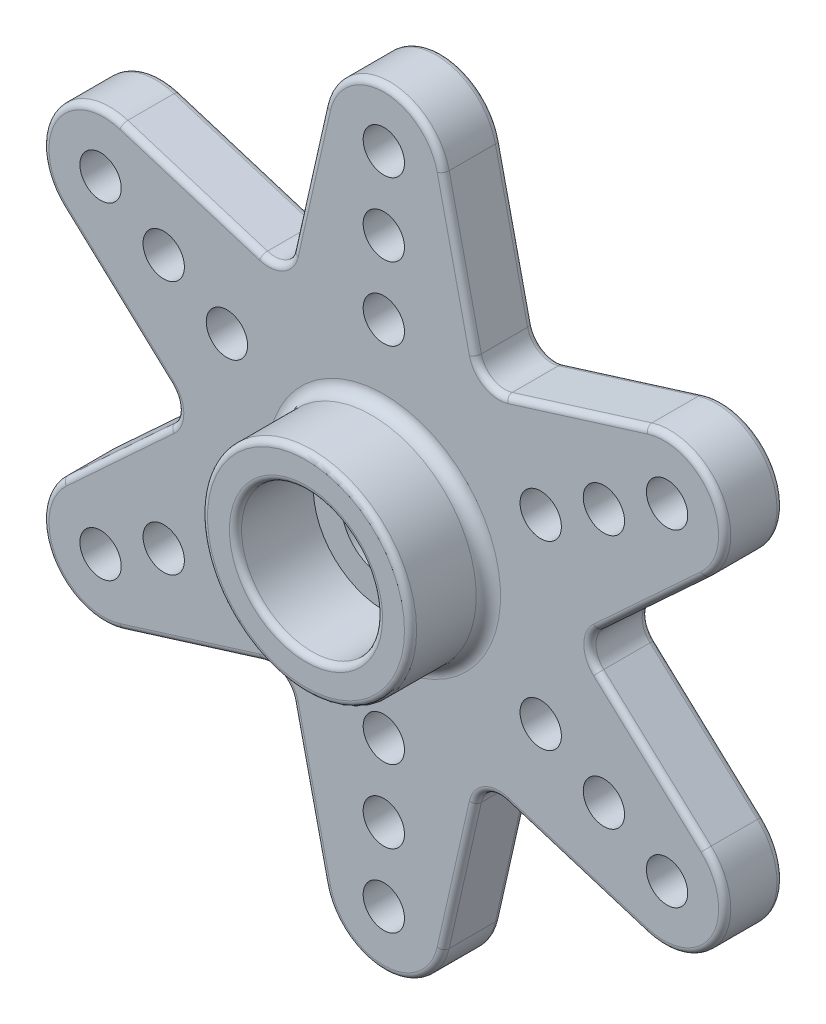
SolidWorks part; units mm, degrees
ref_plane "Front Plane" through (0, 0, 0) normal (0, 0, 1) x (1, 0, 0)
ref_plane "Top Plane" through (0, 0, 0) normal (0, 1, 0) x (1, 0, 0)
ref_plane "Right Plane" through (0, 0, 0) normal (1, 0, 0) x (0, 0, -1)
sketch "Sketch1" plane through (0, 0, 0) normal (0, 0, 1) x (1, 0, 0)
  line L0 (0, 13.3) -> (0, -13.3) construction
  line L1 (-11.5181, 6.65) -> (11.5181, -6.65) construction
  line L2 (11.5181, 6.65) -> (-11.5181, -6.65) construction
  line L3 (-4, -6.9282) -> (-2.4387, -13.8501)
  line L4 (2.4387, 13.8501) -> (4, 6.9282)
  line L5 (4, 6.9282) -> (10.7751, 9.037)
  line L6 (13.2139, 4.813) -> (8, 0)
  line L7 (8, 0) -> (13.2139, -4.813)
  line L8 (10.7751, -9.037) -> (4, -6.9282)
  line L9 (4, -6.9282) -> (2.4387, -13.8501)
  line L10 (-10.7751, -9.037) -> (-4, -6.9282)
  line L11 (-8, 0) -> (-13.2139, -4.813)
  line L12 (-13.2139, 4.813) -> (-8, 0)
  line L13 (-4, 6.9282) -> (-10.7751, 9.037)
  line L14 (-2.4387, 13.8501) -> (-4, 6.9282)
  line L15 (-4, 6.9282) -> (4, 6.9282) construction
  line L16 (-8, 0) -> (-4, 6.9282) construction
  line L17 (-8, 0) -> (-4, -6.9282) construction
  line L18 (-4, -6.9282) -> (4, -6.9282) construction
  arc A0 (-2.4387, 13.8501) -> (2.4387, 13.8501) centre (0, 13.3) cw
  arc A1 (10.7751, 9.037) -> (13.2139, 4.813) centre (11.5181, 6.65) cw
  arc A2 (13.2139, -4.813) -> (10.7751, -9.037) centre (11.5181, -6.65) cw
  arc A3 (2.4387, -13.8501) -> (-2.4387, -13.8501) centre (0, -13.3) cw
  arc A4 (-13.2139, -4.813) -> (-10.7751, -9.037) centre (-11.5181, -6.65) ccw
  arc A5 (-10.7751, 9.037) -> (-13.2139, 4.813) centre (-11.5181, 6.65) ccw
  circle A6 centre (0, 0) radius 1.75
  dimension "D1" = 26.6
  dimension "D2" = 2.5
  dimension "D3" = 8
  dimension "D5" = 3.5
  dimension "D4" = 60
extrude "Boss-Extrude1" add sketch "Sketch1" along normal blind 2.4
sketch "Sketch2" plane through (0, 0, 2.4) normal (0, 0, 1) x (1, 0, 0)
  circle A0 centre (0, 0) radius 4.3
  circle A1 centre (0, 0) radius 2.9
  dimension "D1" = 8.6
  dimension "D2" = 5.8
extrude "Boss-Extrude2" add sketch "Sketch2" along normal blind 3.2
sketch "Sketch4" plane through (0, 0, 0) normal (0, 0, -1) x (-1, 0, 0)
  circle A0 centre (0, 0) radius 3.3
  circle A1 centre (0, 0) radius 3.6
  dimension "D1" = 7.2
  dimension "D2" = 6.6
extrude "Boss-Extrude3" add sketch "Sketch4" along normal blind 0.2
sketch "Sketch5" plane through (0, 0, 0) normal (0, 0, -1) x (-1, 0, 0)
  circle A1 centre (0, 0) radius 3.3
  circle A2 centre (0, 0) radius 4
  circle A3 centre (0, 0) radius 3.6 construction
  circle A4 centre (0, 0) radius 3.6
  circle A5 centre (0, 0) radius 3.3 construction
  dimension "D1" = 8
extrude "Cut-Extrude2" cut sketch "Sketch5" against normal blind 0.4
sketch "Sketch6" plane through (0, 0, 0) normal (0, 0, -1) x (-1, 0, 0)
  line L0 (0, 0) -> (0, 1.0197) construction
  circle A1 centre (0, 7.45) radius 0.85
  dimension "D1" = 1.7
  dimension "D2" = 7.45
extrude "Cut-Extrude3" cut sketch "Sketch6" against normal through all
pattern_linear "LPattern1" count 3 spacing 3 along (0, 1, 0) of "Cut-Extrude3"
pattern_circular "CirPattern1" count 6 over 360 about axis through (0, 0, 0) along (0, 0, 1) of "Cut-Extrude3", "LPattern1"
fillet "Fillet3" radius 1 6 edges at (4, -6.9282, 1.2) (-4, -6.9282, 1.2) (-8, 0, 1.2) (-4, 6.9282, 1.2) (4, 6.9282, 1.2) (8, 0, 1.2)
fillet "Fillet1" radius 0.25 50 edges at (4.3, 0, 5.6) (2.9, 0, 5.6) (8.4743, 0, 0) (11.0049, -2.7739, 0) (13.6832, -7.9, 0) (7.9047, -8.1436, 0) (4.2371, -7.3389, 0) (3.1002, -10.9175, 0) (0, -15.8, 0) (-3.1002, -10.9175, 0) (-4.2371, -7.3389, 0) (-7.9047, -8.1436, 0) (-13.6832, -7.9, 0) (-11.0049, -2.7739, 0) (-8.4743, 0, 0) (-11.0049, 2.7739, 0) (-13.6832, 7.9, 0) (-7.9047, 8.1436, 0) (-4.2371, 7.3389, 0) (-3.1002, 10.9175, 0) (0, 15.8, 0) (3.1002, 10.9175, 0) (4.2371, 7.3389, 0) (7.9047, 8.1436, 0) (13.6832, 7.9, 0) (8.4743, 0, 2.4) (11.0049, -2.7739, 2.4) (13.6832, -7.9, 2.4) (7.9047, -8.1436, 2.4) (4.2371, -7.3389, 2.4) (3.1002, -10.9175, 2.4) (0, -15.8, 2.4) (-3.1002, -10.9175, 2.4) (-4.2371, -7.3389, 2.4) (-7.9047, -8.1436, 2.4) (-13.6832, -7.9, 2.4) (-11.0049, -2.7739, 2.4) (-8.4743, 0, 2.4) (-11.0049, 2.7739, 2.4) (-13.6832, 7.9, 2.4) (-7.9047, 8.1436, 2.4) (-4.2371, 7.3389, 2.4) (-3.1002, 10.9175, 2.4) (0, 15.8, 2.4) (3.1002, 10.9175, 2.4) (4.2371, 7.3389, 2.4) (7.9047, 8.1436, 2.4) (13.6832, 7.9, 2.4) (11.0049, 2.7739, 0) (11.0049, 2.7739, 2.4)
fillet "Fillet2" radius 0.5 1 edges at (-4.3, 0, 2.4)
